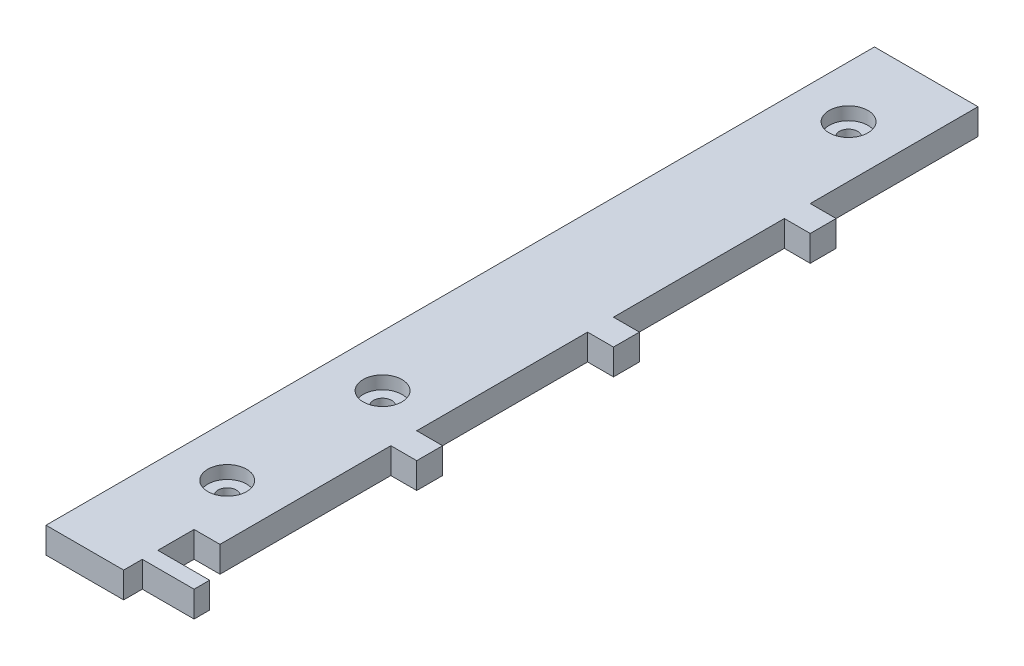
SolidWorks part; units mm, degrees
ref_plane "Front Plane" through (0, 0, 0) normal (0, 0, 1) x (1, 0, 0)
ref_plane "Top Plane" through (0, 0, 0) normal (0, 1, 0) x (1, 0, 0)
ref_plane "Right Plane" through (0, 0, 0) normal (1, 0, 0) x (0, 0, -1)
sketch "Sketch1" plane through (0, 0, 0) normal (0, 1, 0) x (1, 0, 0)
  line L0 (0, 0) -> (31.75, 0)
  line L1 (0, 0) -> (0, 203.2)
  line L2 (31.75, 0) -> (31.75, 203.2)
  line L3 (0, 203.2) -> (31.75, 203.2)
  dimension "D1" = 31.75
  dimension "D2" = 203.2
extrude "Boss-Extrude1" add sketch "Sketch1" along normal blind 6.35
sketch "Sketch2" plane through (0, 6.35, 0) normal (0, 1, 0) x (1, 0, 0)
  line L0 (31.75, 0) -> (31.75, 203.2) construction
  line L1 (31.75, 203.2) -> (25.4, 203.2)
  line L2 (31.75, 203.2) -> (31.75, 162.052)
  line L3 (31.75, 162.052) -> (25.4, 162.052)
  line L4 (25.4, 203.2) -> (25.4, 162.052)
  line L5 (31.75, 155.702) -> (25.4, 155.702)
  line L6 (31.75, 155.702) -> (31.75, 113.792)
  line L7 (31.75, 113.792) -> (25.4, 113.792)
  line L8 (25.4, 155.702) -> (25.4, 113.792)
  line L9 (31.75, 107.442) -> (31.75, 17.272)
  line L10 (31.75, 107.442) -> (25.4, 107.442)
  line L12 (31.75, 65.532) -> (25.4, 65.532)
  line L13 (25.4, 107.442) -> (25.4, 65.532)
  line L18 (31.75, 0) -> (19.05, 0)
  line L19 (31.75, 0) -> (31.75, 4.572)
  line L20 (31.75, 4.572) -> (19.05, 4.572)
  line L21 (19.05, 0) -> (19.05, 4.572)
  line L22 (31.75, 8.382) -> (19.05, 8.382)
  line L23 (31.75, 8.382) -> (31.75, 17.272)
  line L24 (31.75, 17.272) -> (19.05, 17.272)
  line L25 (19.05, 8.382) -> (19.05, 17.272)
  line L26 (31.75, 59.182) -> (25.4, 59.182)
  line L29 (25.4, 59.182) -> (25.4, 17.272)
  dimension "D1" = 4.572
  dimension "D2" = 3.81
  dimension "D3" = 8.89
  dimension "D4" = 12.7
  dimension "D5" = 12.7
  dimension "D6" = 41.91
  dimension "D7" = 6.35
  dimension "D8" = 6.35
  dimension "D9" = 6.35
  dimension "D10" = 6.35
  dimension "D11" = 41.91
  dimension "D12" = 6.35
  dimension "D13" = 41.91
  dimension "D14" = 6.35
extrude "Cut-Extrude1" cut sketch "Sketch2" against normal through all
hole_wizard "CBORE for #8 Binding Head Machine Screw1" positions "Sketch3" profile "Sketch4" counterbore size "#8" standard "ANSI Inch" end condition through all
sketch "Sketch3" plane through (0, 6.35, 0) normal (0, 1, 0) x (1, 0, 0)
  line L0 (0, 203.2) -> (0, 0) construction
  line L1 (0, 0) -> (19.05, 0) construction
  line L2 (25.4, 203.2) -> (0, 203.2) construction
  point P0 (12.7, 31.75)
  point P7 (12.7, 69.85)
  point P10 (12.7, 184.15)
  dimension "D1" = 12.7
  dimension "D2" = 31.75
  dimension "D3" = 38.1
  dimension "D4" = 19.05
sketch "Sketch4" plane through (12.7, 6.35, -31.75) normal (1, 0, 0) x (0, 0, 1)
  line L0 (0, 0) -> (0, 6.35)
  line L1 (0, 6.35) -> (2.2479, 6.35)
  line L3 (2.2479, 6.35) -> (2.2479, 3.175)
  line L4 (2.2479, 3.175) -> (4.7625, 3.175)
  line L5 (4.7625, 3.175) -> (4.7625, 0)
  line L7 (4.7625, 0) -> (0, 0)
  line L11 (0, -6.35) -> (0, 107.95) construction
  dimension "Thru Hole Dia." = 4.4958
  dimension "Thru Hole Depth" = 6.35
  dimension "C'Bore Dia." = 9.525
  dimension "C'Bore Depth" = 3.175
